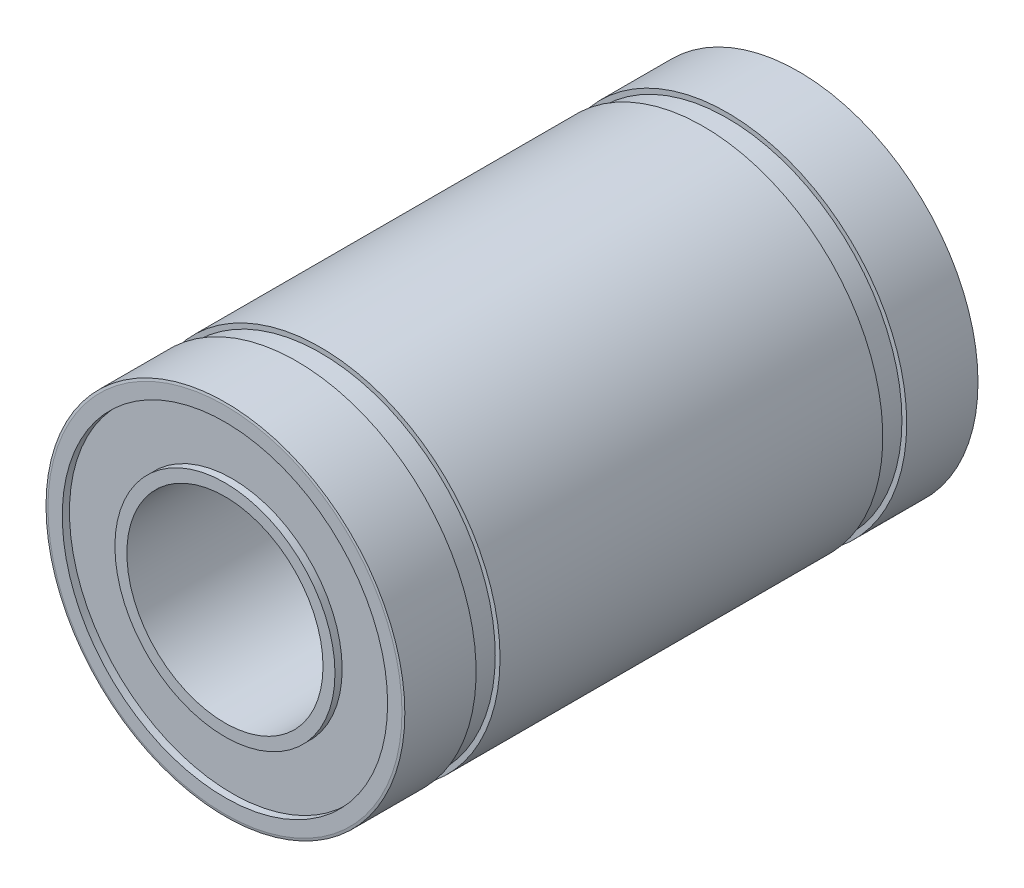
SolidWorks part; units mm, degrees
ref_plane "Alzado" through (0, 0, 0) normal (0, 0, 1) x (1, 0, 0)
ref_plane "Planta" through (0, 0, 0) normal (0, 1, 0) x (1, 0, 0)
ref_plane "Vista lateral" through (0, 0, 0) normal (1, 0, 0) x (0, 0, -1)
sketch "Croquis1" plane through (0, 0, 0) normal (0, 0, 1) x (1, 0, 0)
  circle A0 centre (0, 0) radius 7.5
  circle A1 centre (0, 0) radius 4.1
  dimension "D1" = 15
  dimension "D2" = 8.2
extrude "Saliente-Extruir1" add sketch "Croquis1" along normal blind 24
sketch "Croquis2" plane through (0, 0, 0) normal (0, 1, 0) x (1, 0, 0)
  line L0 (-7.5, -0.02) -> (-7.4, 0)
  line L1 (-7.5, 0) -> (-7.5, -24) construction
  line L2 (7.5, 0) -> (-7.5, 0) construction
  line L3 (-7.4, 0) -> (-6.8, 0)
  line L4 (-6.8, 0) -> (-6.8, -0.3)
  line L5 (-6.8, -0.3) -> (-4.6, -0.3)
  line L6 (-4.6, -0.3) -> (-4.6, 0)
  line L7 (-4.6, 0) -> (-4.1, 0)
  line L8 (-4.1, 0) -> (-4.1, 0.7)
  line L9 (-4.1, 0.7) -> (-7.5, 0.7)
  line L10 (-7.5, 0.7) -> (-7.5, -0.02)
  line L11 (-7.5, -12) -> (7.5, -12) construction
  line L12 (7.5, -24) -> (7.5, 0) construction
  line L13 (-7.5, -24.7) -> (-7.5, -23.98)
  line L14 (-4.1, -24.7) -> (-7.5, -24.7)
  line L15 (-4.1, -24) -> (-4.1, -24.7)
  line L16 (-4.6, -24) -> (-4.1, -24)
  line L17 (-4.6, -23.7) -> (-4.6, -24)
  line L18 (-6.8, -23.7) -> (-4.6, -23.7)
  line L19 (-6.8, -24) -> (-6.8, -23.7)
  line L20 (-7.4, -24) -> (-6.8, -24)
  line L21 (-7.5, -23.98) -> (-7.4, -24)
  line L22 (-7.3, -4) -> (-7.3, -20) construction
  line L23 (-7.7, -3) -> (-7.3, -3)
  line L24 (-7.7, -3) -> (-7.7, -4)
  line L25 (-7.7, -4) -> (-7.3, -4)
  line L26 (-7.3, -3) -> (-7.3, -4)
  line L27 (-7.7, -3) -> (-7.3, -4) construction
  line L28 (-7.7, -4) -> (-7.3, -3) construction
  line L29 (-7.7, -21) -> (-7.3, -21)
  line L30 (-7.7, -21) -> (-7.7, -20)
  line L31 (-7.7, -20) -> (-7.3, -20)
  line L32 (-7.3, -21) -> (-7.3, -20)
  line L33 (-7.7, -21) -> (-7.3, -20) construction
  line L34 (-7.7, -20) -> (-7.3, -21) construction
  line L35 (-7.5, -24) -> (7.5, -24) construction
  line L36 (4.1, 0) -> (-4.1, 0) construction
  line L37 (0, -24) -> (0, 0) construction
  point P27 (-7.5, -3.5)
  point P32 (-7.5, -20.5)
  dimension "D1" = 0.6
  dimension "D2" = 0.5
  dimension "D3" = 0.1
  dimension "D4" = 0.02
  dimension "D5" = 0.3
  dimension "D6" = 1
  dimension "D7" = 1
  dimension "D8" = 1
  dimension "D9" = 3
  dimension "D10" = 3
  dimension "D11" = 0.2
  dimension "D12" = 7.5
revolve "Cortar-Revolución1" cut sketch "Croquis2" angle 360 about axis through (0, 0, 24) along (0, 0, -1)
